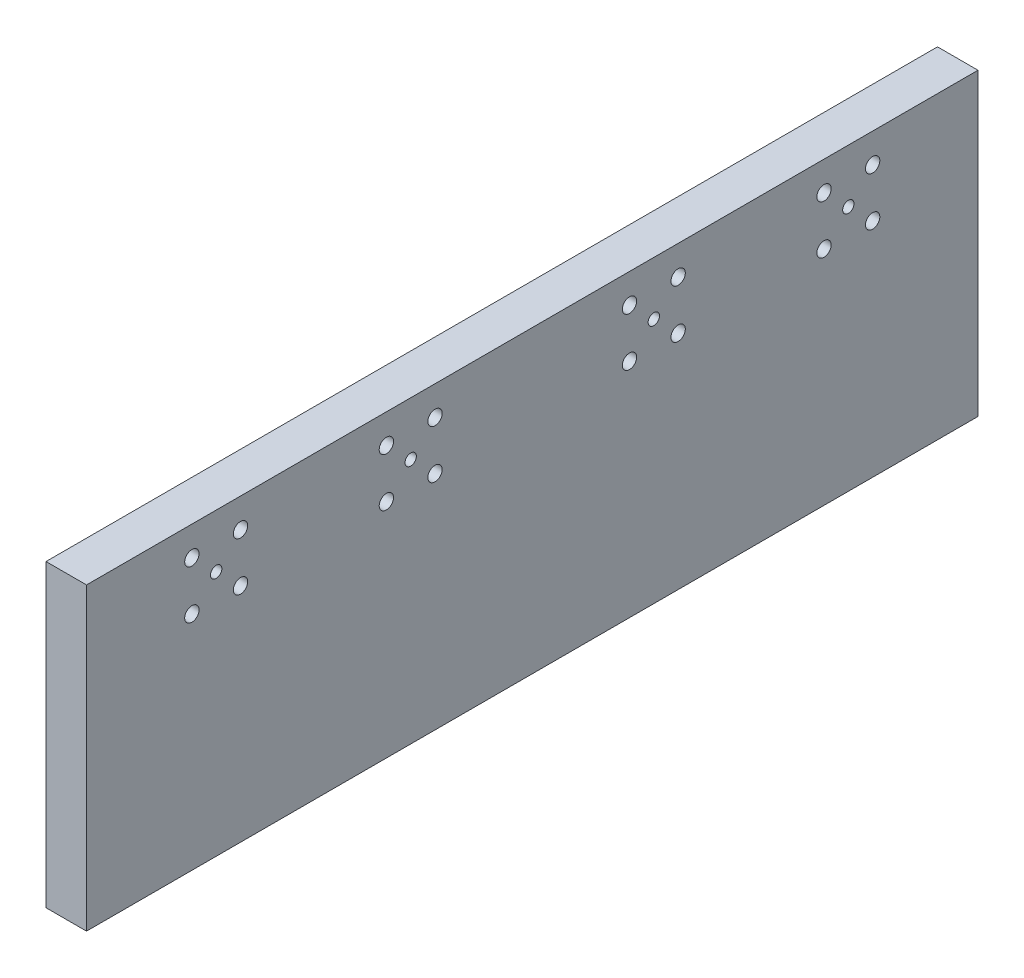
SolidWorks part; units mm, degrees
ref_plane "Front Plane" through (0, 0, 0) normal (0, 0, 1) x (1, 0, 0)
ref_plane "Top Plane" through (0, 0, 0) normal (0, 1, 0) x (1, 0, 0)
ref_plane "Right Plane" through (0, 0, 0) normal (1, 0, 0) x (0, 0, -1)
sketch "Sketch1" plane through (0, 0, 0) normal (0, 1, 0) x (1, 0, 0)
  line L1 (0, 0) -> (12.7, 0)
  line L2 (0, 0) -> (0, -279.4)
  line L3 (0, -279.4) -> (12.7, -279.4)
  line L4 (12.7, 0) -> (12.7, -279.4)
  dimension "D1" = 279.4
  dimension "D2" = 12.7
extrude "Boss-Extrude1" add sketch "Sketch1" along normal blind 93.98
sketch "Sketch2" plane through (12.7, 0, 0) normal (1, 0, 0) x (0, 0, -1)
  line L1 (-279.4, 93.98) -> (-279.4, 0) construction
  line L2 (-279.4, 0) -> (0, 0) construction
  line L3 (-271.7508, 77.216) -> (-43.3929, 77.216)
  circle A0 centre (-238.76, 77.216) radius 1.778
  circle A1 centre (-177.8, 77.216) radius 1.778
  circle A2 centre (-101.6, 77.216) radius 1.778
  circle A3 centre (-40.64, 77.216) radius 1.778
  circle A4 centre (-246.38, 84.836) radius 2.0828
  circle A5 centre (-231.14, 84.836) radius 2.0828
  circle A10 centre (-185.42, 84.836) radius 2.0828
  circle A11 centre (-170.18, 84.836) radius 2.0828
  circle A12 centre (-109.22, 84.836) radius 2.0828
  circle A15 centre (-93.98, 84.836) radius 2.0828
  circle A18 centre (-33.02, 84.836) radius 2.0828
  circle A19 centre (-48.26, 84.836) radius 2.0828
  circle A20 centre (-48.26, 69.596) radius 2.0828
  circle A21 centre (-33.02, 69.596) radius 2.0828
  circle A22 centre (-93.98, 69.596) radius 2.0828
  circle A23 centre (-109.22, 69.596) radius 2.0828
  circle A24 centre (-170.18, 69.596) radius 2.0828
  circle A25 centre (-185.42, 69.596) radius 2.0828
  circle A26 centre (-231.14, 69.596) radius 2.0828
  circle A27 centre (-246.38, 69.596) radius 2.0828
  point P47 (-40.64, 77.216)
  point P48 (-101.6, 77.216)
  point P49 (-177.8, 77.216)
  point P50 (-238.76, 77.216)
  dimension "D3" = 60.96
  dimension "D4" = 76.2
  dimension "D5" = 60.96
  dimension "D9" = 4.1656
  dimension "D6" = 3.556
  dimension "D2" = 40.64
  dimension "D7" = 77.216
  dimension "D8" = 7.62
  dimension "D10" = 7.62
  dimension "D13" = 7.62
  dimension "D14" = 7.62
  dimension "D15" = 7.62
  dimension "D16" = 7.62
  dimension "D17" = 7.62
  dimension "D18" = 7.62
  dimension "D19" = 7.62
extrude "Cut-Extrude1" cut sketch "Sketch2" against normal through all contours A4 | A5 | L3 A0 | L3 A0 | A27 | A26 | L3 A1 | L3 A1 | A10 | A11 | A24 | A25 | L3 A2 | L3 A2 | A23 | A15 | A12 | A20 | L3 A3 | L3 A3 | A19 | A18 | A21 | A22
hole_wizard "CBORE for #8 Binding Head Machine Screw1" positions "Sketch5" profile "Sketch6" counterbore size "#8" standard "ANSI Inch" end condition through all
sketch "Sketch5" plane through (0, 0, 0) normal (-1, 0, 0) x (0, 0, 1)
  point P0 (246.38, 84.836)
  point P3 (246.38, 69.596)
  point P6 (231.14, 69.596)
  point P9 (231.14, 84.836)
  point P12 (185.42, 69.596)
  point P15 (185.42, 84.836)
  point P18 (170.18, 84.836)
  point P21 (170.18, 69.596)
  point P24 (109.22, 69.596)
  point P27 (93.98, 69.596)
  point P30 (93.98, 84.836)
  point P33 (109.22, 84.836)
  point P36 (48.26, 69.596)
  point P39 (33.02, 69.596)
  point P42 (33.02, 84.836)
  point P45 (48.26, 84.836)
sketch "Sketch6" plane through (0, 84.836, 246.38) normal (0, 1, 0) x (0, 0, 1)
  line L0 (0, 0) -> (0, 12.7)
  line L1 (0, 12.7) -> (2.2479, 12.7)
  line L3 (2.2479, 12.7) -> (2.2479, 2.667)
  line L4 (2.2479, 2.667) -> (4.7625, 2.667)
  line L5 (4.7625, 2.667) -> (4.7625, 0)
  line L7 (4.7625, 0) -> (0, 0)
  line L11 (0, -6.35) -> (0, 107.95) construction
  dimension "Thru Hole Dia." = 4.4958
  dimension "Thru Hole Depth" = 12.7
  dimension "C'Bore Dia." = 9.525
  dimension "C'Bore Depth" = 2.667
sketch "Sketch7" plane through (0, 0, 0) normal (0, -1, 0) x (1, 0, 0)
  line L0 (0, 279.4) -> (12.7, 279.4) construction
  point P0 (6.35, 254)
  point P1 (6.35, 177.8)
  point P2 (6.35, 101.6)
  point P3 (6.35, 25.4)
  point P6 (6.35, 279.4)
  dimension "D1" = 25.4
  dimension "D2" = 76.2
  dimension "D3" = 76.2
  dimension "D4" = 76.2
hole_wizard "1/4-20 Tapped Hole1" positions "Sketch8" profile "Sketch9" tap size "1/4-20" standard "ANSI Inch"
sketch "Sketch8" plane through (0, 0, 0) normal (0, -1, 0) x (-1, 0, 0)
  point P0 (-6.35, -25.4)
  point P3 (-6.35, -101.6)
  point P6 (-6.35, -177.8)
  point P9 (-6.35, -254)
sketch "Sketch9" plane through (6.35, 0, 25.4) normal (1, 0, 0) x (0, 0, -1)
  line L0 (0, 0) -> (0, 26.9338)
  line L1 (0, 26.9338) -> (2.5527, 25.4)
  line L2 (2.5527, 25.4) -> (2.5527, 0)
  line L5 (2.5527, 0) -> (0, 0)
  line L10 (0, 26.9338) -> (-2.5527, 25.4) construction
  line L11 (0, -6.35) -> (0, 107.95) construction
  dimension "Tap Drill Dia." = 5.1054
  dimension "Tap Drill Depth" = 25.4
  dimension "Drill Angle" = 118
